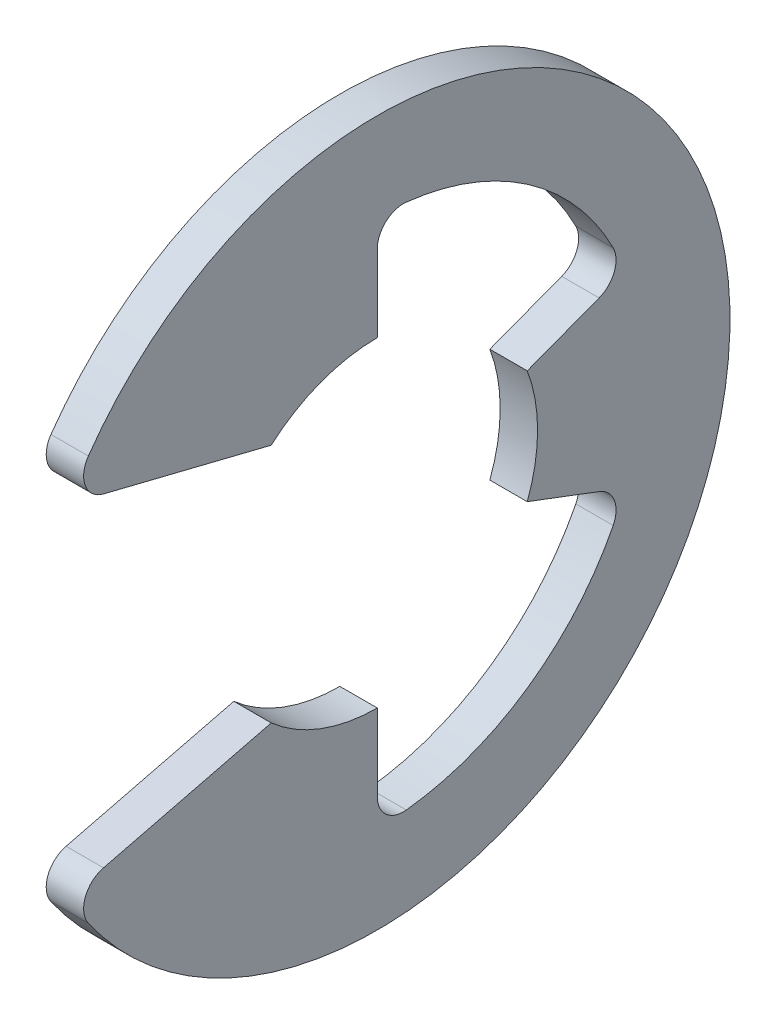
SolidWorks part; units mm, degrees
ref_plane "Front" through (0, 0, 0) normal (0, 0, 1) x (1, 0, 0)
ref_plane "Top" through (0, 0, 0) normal (0, 1, 0) x (1, 0, 0)
ref_plane "Right" through (0, 0, 0) normal (1, 0, 0) x (0, 0, -1)
sketch "Sketch1" plane through (0, 0, 0) normal (1, 0, 0) x (0, 0, -1)
  line L0 (-7.3368, -4.0533) -> (-2.5201, -2.8575)
  line L1 (-7.3368, 4.0533) -> (-2.5201, 2.8575)
  line L2 (0, -3.81) -> (0, -6.2926)
  line L3 (0, 3.81) -> (0, 6.2926)
  line L4 (3.5639, -1.347) -> (5.8862, -2.2248)
  line L5 (3.5639, 1.347) -> (5.8862, 2.2248)
  line L6 (0, 0) -> (-8.636, 0) construction
  line L7 (3.5639, 1.347) -> (3.5639, -1.347) construction
  line L8 (0, -3.81) -> (-2.5201, -2.8575) construction
  line L9 (0, 8.382) -> (0, -8.382) construction
  circle A1 centre (0, 0) radius 8.636 construction
  circle A2 centre (0, 0) radius 3.81 construction
  arc A3 (-7.3368, -4.0533) -> (-7.3368, 4.0533) centre (0, 0) ccw
  arc A4 (-2.5201, -2.8575) -> (0, -3.81) centre (0, 0) ccw
  arc A5 (-2.5201, 2.8575) -> (0, 3.81) centre (0, 0) cw
  arc A6 (3.5639, 1.347) -> (3.5639, -1.347) centre (0, 0) cw
  arc A7 (0, -6.2926) -> (5.8862, -2.2248) centre (0, 0) ccw
  arc A8 (5.8862, 2.2248) -> (0, 6.2926) centre (0, 0) ccw
  dimension "D" = 7.62
  dimension "D1" = 6.2926
  dimension "OD" = 16.764
  dimension "D2" = 4.3322
  dimension "D3" = 5.715
extrude "Extrude1" add sketch "Sketch1" along normal mid plane 0.889
fillet "Fillet1" radius 0.6223 6 edges at (0, -6.2926, 0) (0, 6.2926, 0) (0, -4.0533, 7.3368) (0, 4.0533, 7.3368) (0, -2.2248, -5.8862) (0, 2.2248, -5.8862)
sketch "Sketch3" plane through (0, 0, 0) normal (0, 1, 0) x (1, 0, 0)
  line L0 (0.4953, 4.7625) -> (0.4953, 3.8481)
  line L1 (0.4953, 3.8481) -> (-0.4953, 3.8481)
  line L2 (-0.4953, 3.8481) -> (-0.4953, 4.7625)
  line L3 (-0.4953, 4.7625) -> (-10.6489, 4.7625)
  line L4 (4.21, 0) -> (4.21, 4.3053)
  line L5 (-10.6489, 4.7625) -> (-10.6489, 0)
  line L6 (-10.6489, 0) -> (4.21, 0)
  line L8 (4.21, 0) -> (4.21, 4.7625) construction
  line L9 (4.21, 4.7625) -> (0.4953, 4.7625) construction
  line L10 (4.21, 0) -> (17.2631, 0) construction
  line L11 (4.21, 4.3053) -> (3.7528, 4.7625)
  line L12 (3.7528, 4.7625) -> (0.4953, 4.7625)
  point P2 (0, 3.8481)
  point P5 (0.4953, 4.3053)
  dimension "D2" = 14.859
  dimension "D1" = 3.7147
  dimension "D3" = 45
revolve "Revolve2" [suppressed] add sketch "Sketch3" angle 360 about L10
equation "\"D2@Sketch3\" = \"W@Sketch3\"*15"
equation "\"D1@Sketch3\" = \"D2@Sketch3\"/4"
equation "\"D1@Sketch1\" = (\"OD@Sketch1\"+\"D@Sketch1\")/3.875"
equation "\"D3@Sketch1\" = \"D@Sketch1\"*.75"
equation "\"D1@Fillet1\" = \"D1@Extrude1\"*.7"
